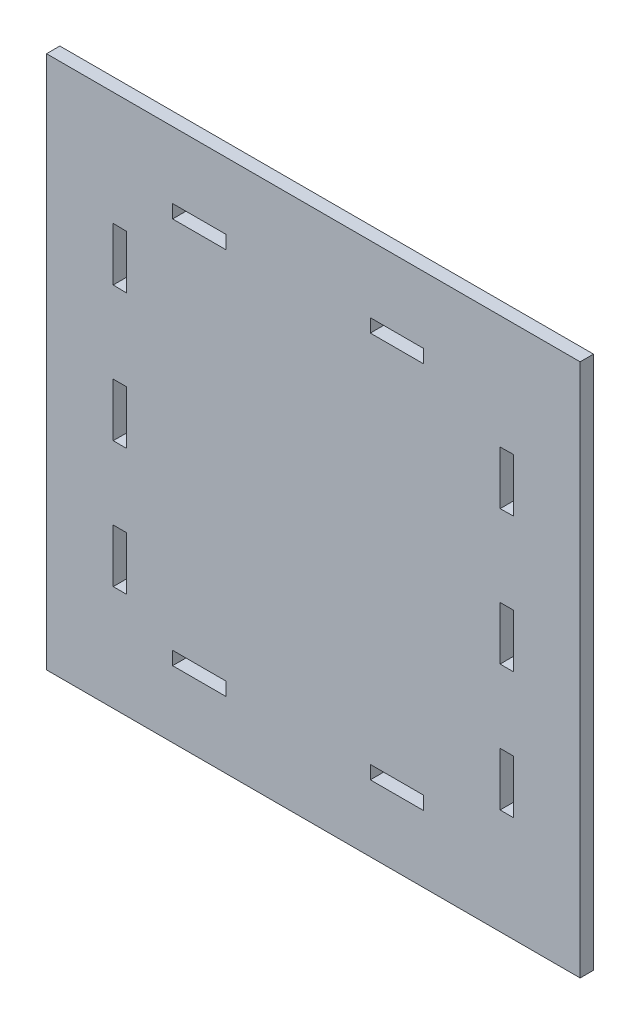
SolidWorks part; units mm, degrees
ref_plane "Front Plane" through (0, 0, 0) normal (0, 0, 1) x (1, 0, 0)
ref_plane "Top Plane" through (0, 0, 0) normal (0, 1, 0) x (1, 0, 0)
ref_plane "Right Plane" through (0, 0, 0) normal (1, 0, 0) x (0, 0, -1)
sketch "Sketch1" plane through (0, 0, 0) normal (0, 0, 1) x (1, 0, 0)
  line L5 (-75, -75) -> (0, 0) construction
  line L6 (-75, 75) -> (75, -75) construction
  line L7 (-52.7387, 75) -> (-52.7387, 70)
  line L8 (-32.7387, 75) -> (-32.7387, 70)
  line L9 (-52.7387, 70) -> (-32.7387, 70)
  line L11 (21.3609, 75) -> (21.3609, 70)
  line L12 (41.3609, 75) -> (41.3609, 70)
  line L13 (21.3609, 70) -> (41.3609, 70)
  line L15 (-75, 57.4357) -> (-70.001, 57.3354)
  line L16 (-75, 37.4357) -> (-70.001, 37.3354)
  line L17 (-70.001, 57.3354) -> (-70.001, 37.3354)
  line L19 (-75, 6.8909) -> (-70, 6.8909)
  line L20 (-75, -13.1091) -> (-70, -13.1091)
  line L21 (-70, 6.8909) -> (-70, -13.1091)
  line L22 (-75, -40.4642) -> (-70, -40.4642)
  line L24 (-70, -40.4642) -> (-70, -60.4642)
  line L25 (-75, -60.4642) -> (-70, -60.4642)
  line L26 (-70, 0) -> (70, 0) construction
  line L27 (0, 75) -> (0, -75) construction
  line L28 (41.3609, -75) -> (41.3609, -70)
  line L29 (21.3609, -75) -> (21.3609, -70)
  line L30 (21.3609, -70) -> (41.3609, -70)
  line L31 (-32.7387, -75) -> (-32.7387, -70)
  line L32 (-52.7387, -75) -> (-52.7387, -70)
  line L33 (-52.7387, -70) -> (-32.7387, -70)
  line L34 (75, -60.4642) -> (70, -60.4642)
  line L35 (70, -40.4642) -> (70, -60.4642)
  line L36 (75, -40.4642) -> (70, -40.4642)
  line L37 (75, -13.1091) -> (70, -13.1091)
  line L38 (70, 6.8909) -> (70, -13.1091)
  line L39 (75, 6.8909) -> (70, 6.8909)
  line L40 (75, 37.4357) -> (70.001, 37.3354)
  line L41 (70.001, 57.3354) -> (70.001, 37.3354)
  line L42 (75, 57.4357) -> (70.001, 57.3354)
  line L53 (21.3609, 75) -> (41.3609, 75)
  line L54 (-100, -100) -> (100, -100)
  line L55 (-100, -100) -> (-100, 100)
  line L56 (-100, 100) -> (100, 100)
  line L57 (100, -100) -> (100, 100)
  line L58 (-100, -100) -> (0, 0) construction
  line L59 (-100, 100) -> (100, -100) construction
  line L60 (-32.7387, 75) -> (-52.7387, 75)
  line L61 (75, 57.4357) -> (75, 37.4357)
  line L62 (75, 6.8909) -> (75, -13.1091)
  line L63 (75, -40.4642) -> (75, -60.4642)
  line L64 (41.3609, -75) -> (21.3609, -75)
  line L65 (-32.7387, -75) -> (-52.7387, -75)
  line L66 (-75, -60.4642) -> (-75, -40.4642)
  line L67 (-75, -13.1091) -> (-75, 6.8909)
  line L68 (-75, 37.4357) -> (-75, 57.4357)
  line L69 (75, 75) -> (100, 100) construction
  point P0 (0, 0)
  point P6 (0, 0)
  dimension "D13" = 5
  dimension "D1" = 150
  dimension "D2" = 150
  dimension "D3" = 20
  dimension "D4" = 5
  dimension "D5" = 5
  dimension "D6" = 20
  dimension "D7" = 5
  dimension "D8" = 5
  dimension "D9" = 5
  dimension "D10" = 20
  dimension "D11" = 20
  dimension "D12" = 20
  dimension "D14" = 5
  dimension "D15" = 5
  dimension "D16" = 200
  dimension "D17" = 200
extrude "Boss-Extrude1" add sketch "Sketch1" along normal blind 5
